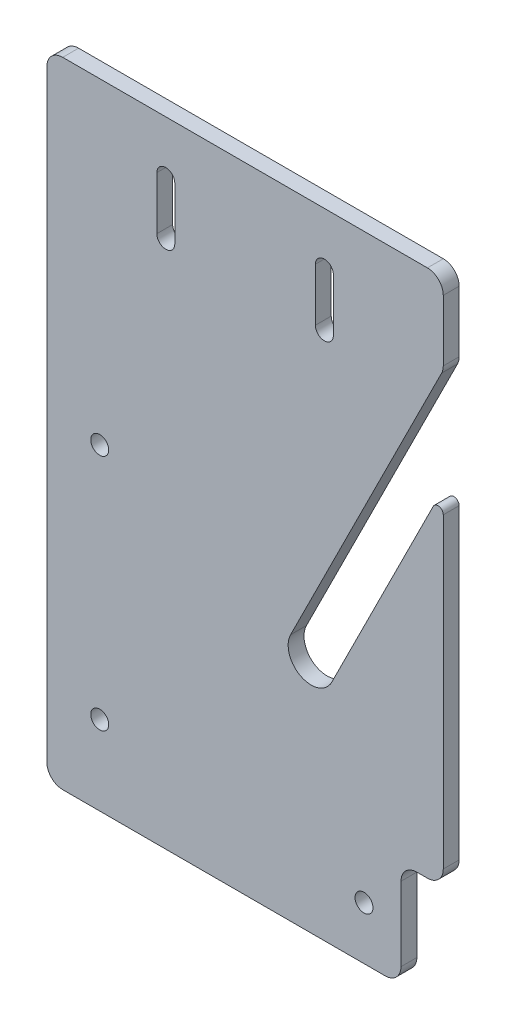
SolidWorks part; units mm, degrees
material "Acrylic (Medium-high impact)"
ref_plane "Front Plane" through (0, 0, 0) normal (0, 0, 1) x (1, 0, 0)
ref_plane "Top Plane" through (0, 0, 0) normal (0, 1, 0) x (1, 0, 0)
ref_plane "Right Plane" through (0, 0, 0) normal (1, 0, 0) x (0, 0, -1)
sketch "Sketch1" plane through (0, 0, 0) normal (0, 0, 1) x (1, 0, 0)
  line L0 (0, 0) -> (0, -120)
  line L1 (0, -120) -> (75, -120)
  line L2 (75, -120) -> (75, 0)
  line L3 (75, 0) -> (0, 0)
  line L4 (56.1092, -53.0546) -> (46.1092, -73.0546)
  line L5 (53.8908, -76.9454) -> (63.8908, -56.9454)
  line L6 (63.8908, -56.9454) -> (75, -34.7269)
  line L7 (56.1092, -53.0546) -> (75, -15.2731)
  circle A0 centre (50, -75) radius 4.35
  circle A1 centre (60, -110) radius 1.7
  circle A2 centre (10, -60) radius 1.7
  circle A3 centre (10, -105) radius 1.7
  circle A6 centre (60, -55) radius 4.35
  dimension "D4" = 8.7
  dimension "D6" = 3.4
  dimension "D8" = 3.4
  dimension "D9" = 3.4
  dimension "D10" = 15
  dimension "D16" = 8.7
  dimension "D1" = 120
  dimension "D2" = 75
  dimension "D3" = 50
  dimension "D5" = 45
  dimension "D7" = 10
  dimension "D12" = 15
  dimension "D13" = 10
  dimension "D15" = 45
  dimension "D17" = 10
  dimension "D18" = 20
extrude "Boss-Extrude1" add sketch "Sketch1" along normal blind 3
fillet "Fillet1" radius 3 5 edges at (0, -120, 1.5) (75, -120, 1.5) (75, 0, 1.5) (0, 0, 1.5) (75, -15.2731, 1.5)
sketch "Sketch2" plane through (0, 0, 3) normal (0, 0, 1) x (1, 0, 0)
  line L0 (72, 0) -> (3, 0) construction
  line L1 (37.5, 0) -> (37.5, -120) construction
  line L2 (3, -120) -> (72, -120) construction
  line L3 (22.5, -10) -> (52.5, -10) construction
  line L4 (20.8, -10) -> (20.8, -20)
  line L5 (24.2, -10) -> (24.2, -20)
  line L6 (50.8, -10) -> (50.8, -20)
  line L7 (54.2, -10) -> (54.2, -20)
  arc A0 (24.2, -10) -> (20.8, -10) centre (22.5, -10) ccw
  arc A1 (54.2, -10) -> (50.8, -10) centre (52.5, -10) ccw
  arc A2 (20.8, -20) -> (24.2, -20) centre (22.5, -20) ccw
  arc A3 (50.8, -20) -> (54.2, -20) centre (52.5, -20) ccw
  point P10 (37.5, -10)
  dimension "D3" = 3.4
  dimension "D4" = 3.4
  dimension "D1" = 30
  dimension "D2" = 110
  dimension "D5" = 10
  dimension "D6" = 10
extrude "Cut-Extrude1" cut sketch "Sketch2" against normal through all
sketch "Sketch3" plane through (0, 0, 3) normal (0, 0, 1) x (1, 0, 0)
  line L0 (75, -117) -> (75, -34.7269) construction
  line L1 (75, -100) -> (67, -100)
  line L2 (75, -100) -> (75, -120)
  line L3 (75, -120) -> (67, -120)
  line L4 (67, -100) -> (67, -120)
  line L5 (3, -120) -> (72, -120) construction
  dimension "D1" = 8
  dimension "D2" = 20
extrude "Cut-Extrude2" cut sketch "Sketch3" against normal through all
fillet "Fillet2" radius 3 3 edges at (75, -100, 1.5) (67, -100, 1.5) (67, -120, 1.5)
fillet "Fillet3" radius 1 1 edges at (75, -34.7269, 1.5)
equation "\"D16@Sketch1\"=\"D4@Sketch1\""
